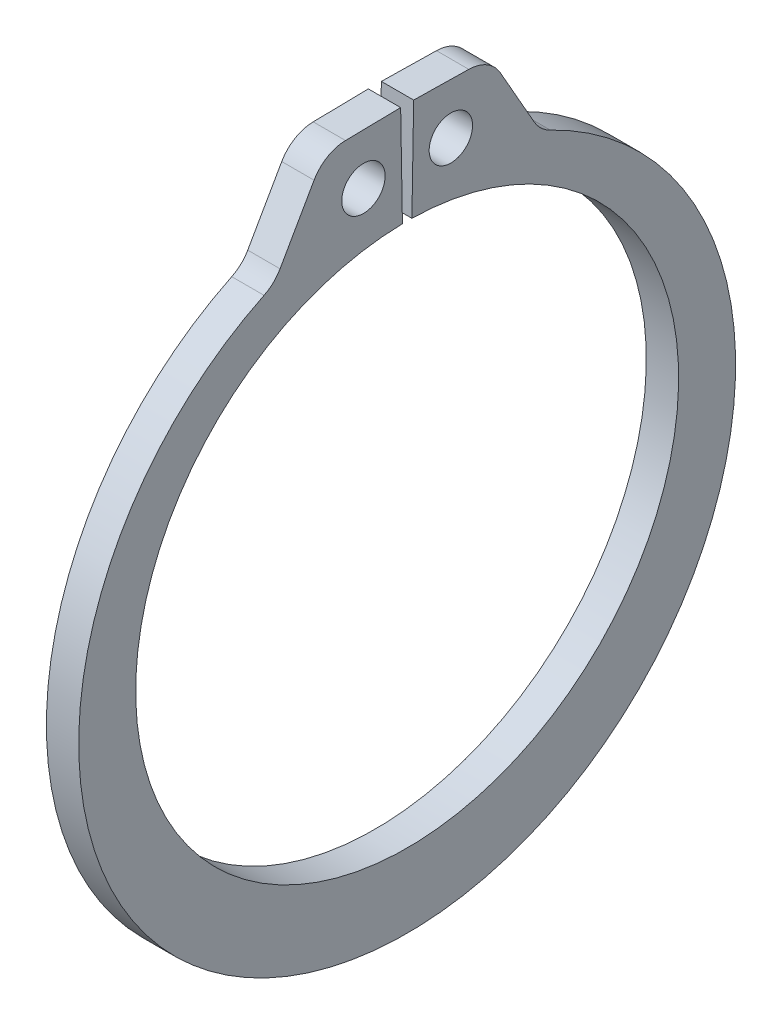
SolidWorks part; units mm, degrees
material "Cast Carbon Steel"
ref_plane "Front" through (0, 0, 0) normal (0, 0, 1) x (1, 0, 0)
ref_plane "Top" through (0, 0, 0) normal (0, 1, 0) x (1, 0, 0)
ref_plane "Right" through (0, 0, 0) normal (1, 0, 0) x (0, 0, -1)
sketch "Sketch1" plane through (0, 0, 0) normal (1, 0, 0) x (0, 0, -1)
  line L0 (0, 0) -> (0, 7.4676) construction
  line L1 (-0.1303, 7.4665) -> (-0.1791, 10.26)
  line L2 (0.1791, 10.26) -> (2.2743, 10.2235)
  line L3 (2.2743, 10.2235) -> (3.6568, 7.7955)
  line L4 (0.1303, 7.4665) -> (0.1791, 10.26)
  line L5 (-0.1791, 10.26) -> (-2.2743, 10.2235)
  line L6 (-2.2743, 10.2235) -> (-3.6568, 7.7955)
  line L7 (-3.6568, 7.7955) -> (-3.1714, 6.7607) construction
  line L8 (3.6568, 7.7955) -> (3.1714, 6.7607) construction
  line L9 (0, -7.4676) -> (0, -9.4996) construction
  line L10 (-2.2743, 10.2235) -> (-0.1303, 7.4665) construction
  line L11 (0, 7.4676) -> (0, 10.2616) construction
  line L12 (-7.4676, 0) -> (7.4676, 0) construction
  circle A0 centre (0, 0) radius 7.4676 construction
  arc A1 (-0.1303, 7.4665) -> (0.1303, 7.4665) centre (0, 0) ccw
  circle A3 centre (0, 0) radius 11.2395 construction
  circle A4 centre (-1.2023, 8.845) radius 0.5969
  circle A5 centre (1.2023, 8.845) radius 0.5969
  arc A6 (-3.6568, 7.7955) -> (3.6568, 7.7955) centre (0, -0.4654) ccw
  point P0 (0, -9.4996)
  dimension "A" = 14.9352
  dimension "D2" = 2.0955
  dimension "L" = 22.479
  dimension "Hole" = 1.1938
  dimension "Smin" = 1.143
  dimension "Smax" = 2.032
  dimension "H" = 2.794
  dimension "Angle" = 1
extrude "Extrude1" add sketch "Sketch1" along normal mid plane 0.889
fillet "Fillet1" radius 1.016 4 edges at (0, 7.7955, 3.6568) (0, 7.7955, -3.6568) (0, 10.2235, 2.2743) (0, 10.2235, -2.2743)
sketch "Sketch2" plane through (0, 0, 0) normal (0, 0, 1) x (1, 0, 0)
  line L0 (-4.9403, 0) -> (12.8397, 0)
  line L1 (12.8397, 0) -> (12.8397, -7.9375)
  line L2 (-0.4953, -7.9375) -> (-4.4704, -7.9375)
  line L3 (12.8397, -7.9375) -> (0.4953, -7.9375)
  line L4 (0.4953, -7.9375) -> (0.4953, -7.4676)
  line L5 (0.4953, -7.4676) -> (-0.4953, -7.4676)
  line L6 (-0.4953, -7.4676) -> (-0.4953, -7.9375)
  line L7 (-0.4953, -7.9375) -> (-4.9403, -7.9375) construction
  line L8 (-4.9403, -7.9375) -> (-4.9403, 0) construction
  line L9 (12.8397, 0) -> (76.391, 0) construction
  line L10 (-4.4704, -7.9375) -> (-4.9403, -7.4676)
  line L11 (-4.9403, -7.4676) -> (-4.9403, 0)
  point P10 (0, -7.4676)
  dimension "D1" = 45
  dimension "Dg" = 14.9352
  dimension "Ds" = 15.875
  dimension "W" = 0.9906
  dimension "D2" = 17.78
  dimension "D3" = 4.445
revolve "Revolve1" [suppressed] add sketch "Sketch2" angle 360 about L9
delete or keep bodies "Body-Delete1" [suppressed] type delete bodies bodies 122
equation "\"D2@Sketch2\" = \"D1@Extrude1\"*20"
equation "\"D3@Sketch2\" = \"D2@Sketch2\"/4"
equation "\"D2@Sketch1\" = \"H@Sketch1\"*.75"
